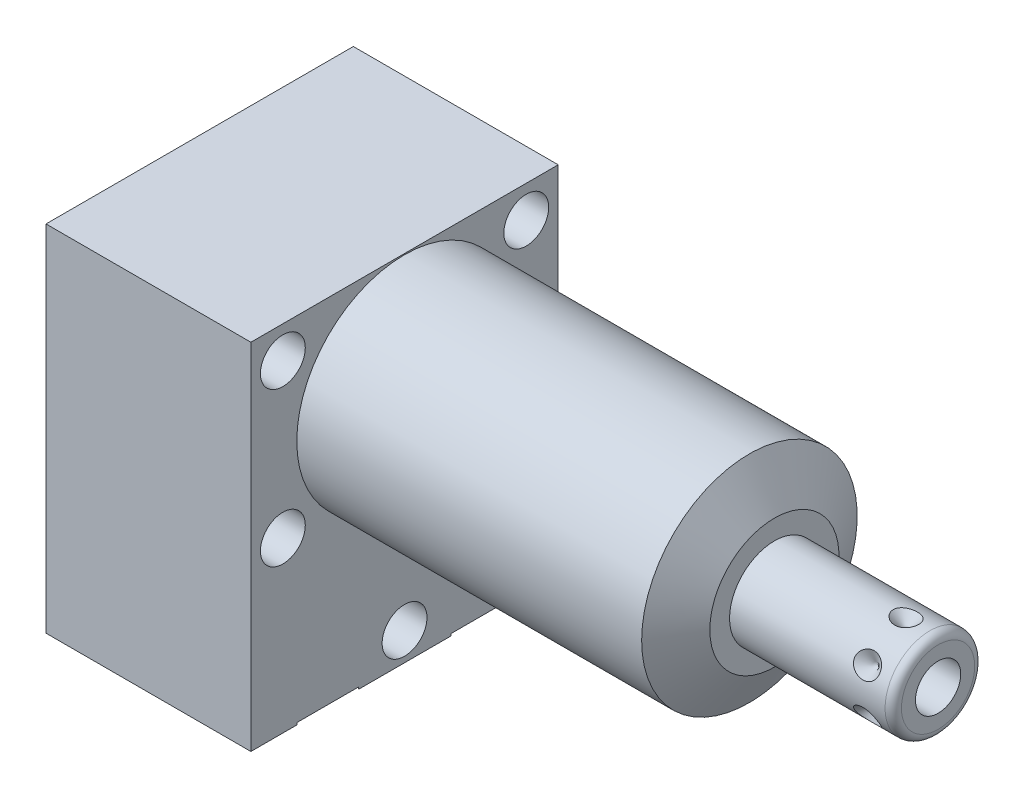
SolidWorks part; units mm, degrees
material "Alloy Steel"
ref_plane "Front Plane" through (0, 0, 0) normal (0, 0, 1) x (1, 0, 0)
ref_plane "Top Plane" through (0, 0, 0) normal (0, 1, 0) x (1, 0, 0)
ref_plane "Right Plane" through (0, 0, 0) normal (1, 0, 0) x (0, 0, -1)
ref_plane "Plane1" through (0, 0, 0) normal (1, 0, 0) x (0, 0, -1)
sketch "Sketch1" plane through (0, 0, 0) normal (1, 0, 0) x (0, 0, -1)
  line L0 (-19.05, 13.4874) -> (-19.05, -30.4546)
  line L1 (-19.05, -30.4546) -> (19.05, -30.4546)
  line L2 (19.05, -30.4546) -> (19.05, 13.4874)
  line L3 (19.05, 13.4874) -> (-19.05, 13.4874)
  line L4 (0, -32.6517) -> (0, 15.6845) construction
  dimension "D1" = 38.1
  dimension "D2" = 43.942
  dimension "D3" = 13.4874
extrude "Extrude1" add sketch "Sketch1" along normal blind 45.847 and the other way blind 25.4
ref_plane "Plane2" through (0, 0, 0) normal (1, 0, 0) x (0, 0, -1)
sketch "Sketch2" plane through (0, 0, 0) normal (1, 0, 0) x (0, 0, -1)
  line L0 (-14.6964, 0) -> (14.6964, 0) construction
  line L5 (19.05, 13.4874) -> (-19.05, 13.4874)
  line L6 (-19.05, 13.4874) -> (-19.05, -30.4546)
  line L7 (-19.05, -30.4546) -> (19.05, -30.4546)
  line L8 (19.05, -30.4546) -> (19.05, 13.4874)
  line L9 (19.05, 13.4874) -> (-19.05, 13.4874)
  line L10 (-19.05, 13.4874) -> (-19.05, -30.4546)
  line L11 (-19.05, -30.4546) -> (19.05, -30.4546)
  line L12 (19.05, -30.4546) -> (19.05, 13.4874)
  circle A0 centre (0, 0) radius 13.3604
  dimension "D1" = 26.7208
  dimension "D2" = 0
extrude "Cut-Extrude1" cut sketch "Sketch2" along normal up to next
ref_plane "Plane3" through (0, 0, 0) normal (0, 0, 1) x (1, 0, 0)
sketch "Sketch3" plane through (0, 0, 0) normal (0, 0, 1) x (1, 0, 0)
  line L0 (42.7527, 13.3604) -> (45.847, 8.001)
  line L1 (42.598, 0) -> (46.0017, 0) construction
  line L2 (45.847, 13.3604) -> (45.847, 8.001)
  line L3 (45.847, 13.3604) -> (42.7527, 13.3604)
  line L4 (45.847, 13.3604) -> (0, 13.3604) construction
  line L5 (45.847, -13.3604) -> (45.847, 13.3604) construction
  dimension "D1" = 30
  dimension "D2" = 16.002
revolve "Cut-Revolve1" cut sketch "Sketch3" angle 360 about L1
ref_plane "Plane4" through (-22.733, -19.8374, 9.525) normal (0, 0, 1) x (0, 1, 0)
sketch "S2D0002" plane through (-22.733, -19.8374, 9.525) normal (0, 0, 1) x (0, 1, 0)
  line L0 (-0.8128, 0) -> (3.7338, 0)
  line L1 (3.7338, 0) -> (3.2938, -2.0701)
  line L2 (3.2938, -2.0701) -> (2.6416, -2.7223)
  line L3 (2.6416, -2.7223) -> (2.6416, -13.97)
  line L4 (2.6416, -13.97) -> (-0.8128, -13.97)
  line L5 (-0.8128, -13.97) -> (-0.8128, 0)
  line L6 (-0.8128, -14.6685) -> (-0.8128, 0.6985) construction
  line L7 (19.8374, -65.4857) -> (19.8374, -22.733) construction
  dimension "D1" = 13.97
  dimension "D2" = 20.6502
revolve "Cut-Revolve2" cut sketch "S2D0002" angle 360 about L6
ref_plane "Plane5" through (-22.733, -19.8374, -9.525) normal (0, 0, 1) x (0, 1, 0)
sketch "Sketch5" plane through (-22.733, -19.8374, -9.525) normal (0, 0, 1) x (0, 1, 0)
  line L0 (-0.8128, 0) -> (3.7338, 0)
  line L1 (3.7338, 0) -> (3.2938, -2.0701)
  line L2 (3.2938, -2.0701) -> (2.6416, -2.7223)
  line L3 (2.6416, -2.7223) -> (2.6416, -13.97)
  line L4 (2.6416, -13.97) -> (-0.8128, -13.97)
  line L5 (-0.8128, -13.97) -> (-0.8128, 0)
  line L6 (-0.8128, -14.6685) -> (-0.8128, 0.6985) construction
  line L7 (19.8374, -65.4857) -> (19.8374, -22.733) construction
  dimension "D1" = 13.97
  dimension "D2" = 20.6502
revolve "Cut-Revolve3" cut sketch "Sketch5" angle 360 about L6
ref_plane "Plane6" through (-8.7376, -30.2006, 9.525) normal (0, 0, 1) x (-1, 0, 0)
sketch "Sketch14" plane through (-25.4, 0, 0) normal (-1, 0, 0) x (0, 0, 1)
  circle A0 centre (-9.525, -20.6502) radius 7.9375
  circle A1 centre (9.525, -20.6502) radius 7.9375
  dimension "D1" = 15.875
extrude "Cut-Extrude2" cut sketch "Sketch14" against normal blind 2.667
sketch "Sketch6" plane through (-8.7376, -30.2006, 9.525) normal (0, 0, 1) x (-1, 0, 0)
  line L0 (16.6624, -43.688) -> (16.6624, 0.254) construction
  line L1 (6.1836, 0) -> (5.641, -2.5527)
  line L2 (5.641, -2.5527) -> (4.9771, -3.2166)
  line L3 (4.9771, -3.2166) -> (4.9771, -17.272)
  line L4 (4.9771, -17.272) -> (0, -17.272)
  line L5 (0, -17.272) -> (0, 0)
  line L6 (0, -18.1356) -> (0, 0.8636) construction
  line L7 (6.1836, 0) -> (9.5237, 0)
  line L8 (9.5237, 0) -> (9.5237, 0.254)
  line L9 (16.6624, 0.254) -> (-8.7376, 0.254) construction
  line L10 (9.5237, 0.254) -> (0, 0.254)
  line L11 (0, 0.254) -> (0, 0)
  dimension "D1" = 19.0475
  dimension "D2" = 0.254
  dimension "D3" = 16.6624
revolve "Cut-Revolve4" cut sketch "Sketch6" angle 360 about L6
ref_plane "Plane7" through (-8.7376, -30.2006, -9.525) normal (0, 0, 1) x (-1, 0, 0)
sketch "Sketch7" plane through (-8.7376, -30.2006, -9.525) normal (0, 0, 1) x (-1, 0, 0)
  line L0 (16.6624, -43.688) -> (16.6624, 0.254) construction
  line L1 (6.1849, 0) -> (5.6423, -2.5527)
  line L2 (5.6423, -2.5527) -> (4.9784, -3.2166)
  line L3 (4.9784, -3.2166) -> (4.9784, -17.272)
  line L4 (4.9784, -17.272) -> (0, -17.272)
  line L5 (0, -17.272) -> (0, 0)
  line L6 (0, -18.1356) -> (0, 0.8636) construction
  line L7 (6.1849, 0) -> (9.5237, 0)
  line L8 (9.5237, 0) -> (-8.7376, 0) construction
  line L9 (9.5237, 0) -> (9.5237, 0.254)
  line L10 (16.6624, 0.254) -> (-8.7376, 0.254) construction
  line L11 (9.5237, 0.254) -> (0, 0.254)
  line L12 (0, 0.254) -> (0, 0)
  dimension "D1" = 16.6624
  dimension "D2" = 9.9568
  dimension "D3" = 19.0475
revolve "Cut-Revolve5" cut sketch "Sketch7" angle 360 about L6
ref_plane "Plane8" through (0, 0, 0) normal (0, 0, 1) x (1, 0, 0)
sketch "Sketch8" plane through (0, 0, 0) normal (0, 0, 1) x (1, 0, 0)
  line L0 (45.847, 0) -> (45.847, 5.5562)
  line L1 (45.847, 5.5562) -> (65.1256, 5.5562)
  line L2 (66.1416, 4.5403) -> (66.1416, 0)
  line L3 (66.1416, 0) -> (45.847, 0)
  line L4 (44.8323, 0) -> (67.1563, 0) construction
  line L5 (45.847, -8.001) -> (45.847, 8.001) construction
  line L6 (-25.4, 13.4874) -> (-25.4, -30.4546) construction
  arc A0 (66.1416, 4.5403) -> (65.1256, 5.5562) centre (65.1256, 4.5403) ccw
  point P0 (45.847, 0)
  dimension "D3" = 1.016
  dimension "D1" = 91.5416
  dimension "D2" = 11.1125
revolve "Revolve1" add sketch "Sketch8" angle 360 about L4
ref_plane "Plane9" through (66.1416, -2.8067, 0) normal (0, 0, 1) x (0, -1, 0)
sketch "S2D0001" plane through (66.1416, -2.8067, 0) normal (0, 0, 1) x (0, -1, 0)
  line L0 (0, 0) -> (0, -10.16)
  line L1 (0, -10.16) -> (-2.8067, -11.8464)
  line L2 (0, 0) -> (-2.8067, 0)
  line L3 (-2.8067, 0) -> (-2.8067, -11.8464)
  line L4 (-2.8067, -12.4388) -> (-2.8067, 0.5923) construction
  line L5 (1.7335, 0) -> (-7.3469, 0) construction
  dimension "D1" = 5.6134
  dimension "D2" = 10.16
  dimension "D3" = 59
revolve "Cut-Revolve6" cut sketch "S2D0001" angle 360 about L4
ref_plane "Plane12" through (62.1792, -5.5562, 0) normal (0, 0, 1) x (-1, 0, 0)
sketch "Sketch12" plane through (62.1792, -5.5562, 0) normal (0, 0, 1) x (-1, 0, 0)
  line L0 (0, 0) -> (1.5875, 0)
  line L1 (1.5875, 0) -> (0, -1.5875)
  line L2 (0, 0) -> (0, -1.5875)
  line L3 (0, -3.434) -> (0, 0.0794) construction
  line L4 (16.3322, 0) -> (-2.9464, 0) construction
  line L5 (-3.9624, -1.016) -> (-3.9624, -10.0965) construction
  dimension "D1" = 3.9624
  dimension "D2" = 45
  dimension "D3" = 3.175
revolve "Cut-Revolve7" cut sketch "Sketch12" angle 360 about L3
pattern_circular "CirPattern1" count 6 over 360 about axis through (45.848, 0, 0) along (-1, 0, 0) of "Cut-Revolve7"
hole_wizard "Hole1" positions "Sketch17" profile "Sketch16" legacy end condition up to next
sketch "Sketch17" plane through (0, 0, 0) normal (1, 0, 0) x (0, 0, -1)
  line L0 (0, 0) -> (0, 17.9298) construction
  line L1 (0, 0) -> (-24.6425, 0) construction
  point P0 (-15.0876, 9.525)
  point P10 (-15.0876, -9.525)
  point P12 (15.0876, 9.525)
  point P13 (15.0876, -9.525)
  point P14 (0, -26.9748)
  dimension "D1" = 9.525
  dimension "D2" = 15.0876
  dimension "D3" = 26.9748
sketch "Sketch16" plane through (0, 9.525, 15.0876) normal (0, 1, 0) x (0, 0, -1)
  line L0 (0, 0) -> (0, 25.4)
  line L1 (0, 25.4) -> (2.7813, 25.4)
  line L2 (2.7813, 25.4) -> (2.7813, 0)
  line L3 (2.7813, 0) -> (0, 0)
  line L4 (0, 110) -> (0, -10) construction
  dimension "Diameter" = 5.5626
  dimension "Depth" = 25.4
sketch "Sketch18" plane through (-8.7376, -30.2006, 9.525) normal (0, 0, 1) x (-1, 0, 0)
  line L0 (-0.6385, -9.5504) -> (23.3703, -9.5504) construction
  line L1 (11.2731, -9.5504) -> (3.5849, -9.5504) construction
  line L3 (13.9954, -17.4879) -> (13.9954, -1.6129) construction
  circle A0 centre (15.7607, -3.3782) radius 1.7653
  dimension "D1" = 3.5306
  dimension "D2" = 12.3444
revolve "Revolve2" add sketch "Sketch18" angle 360 about L0
